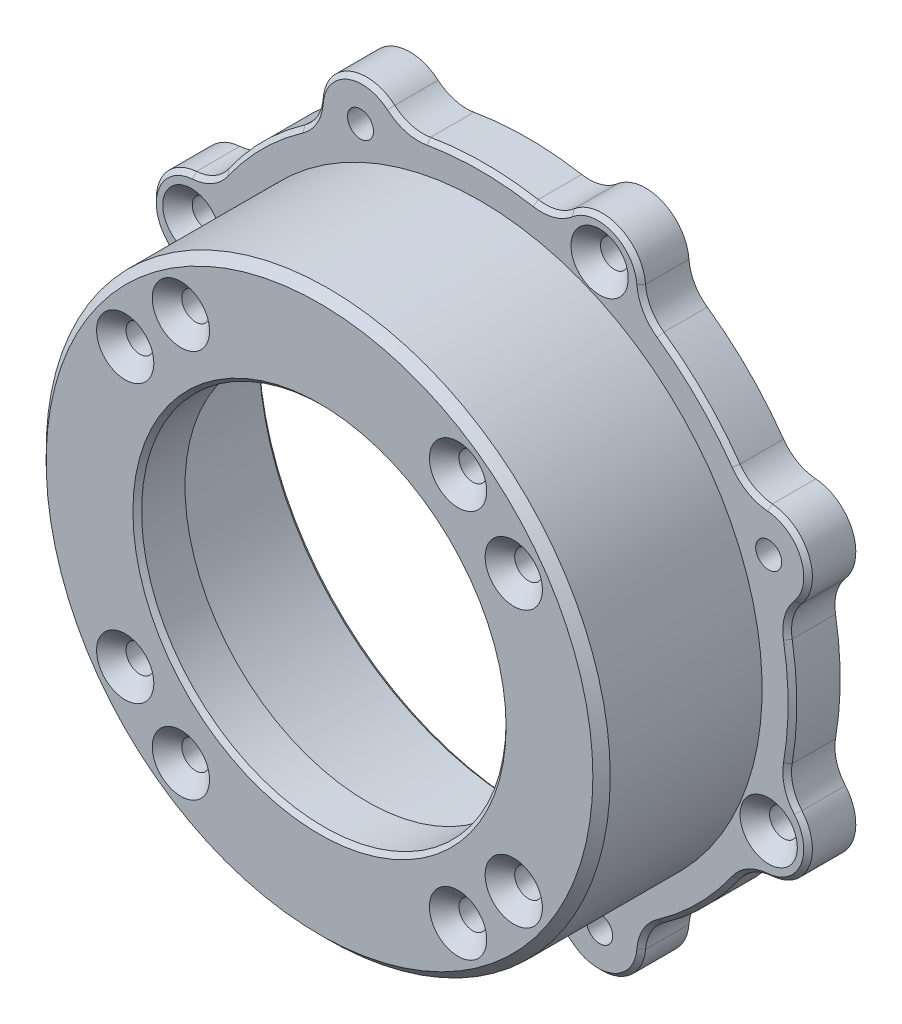
SolidWorks part; units mm, degrees
material "6061 合金"
ref_plane "前视基准面" through (0, 0, 0) normal (0, 0, 1) x (1, 0, 0)
ref_plane "上视基准面" through (0, 0, 0) normal (0, 1, 0) x (1, 0, 0)
ref_plane "右视基准面" through (0, 0, 0) normal (1, 0, 0) x (0, 0, -1)
sketch "草图2" plane through (0, 0, 0) normal (0, 0, 1) x (1, 0, 0)
  circle A0 centre (-15.9693, -22.3882) radius 1.5
  circle A1 centre (-22.3882, -15.9693) radius 1.5
  circle A2 centre (-22.3882, 15.9693) radius 1.5
  circle A3 centre (-15.9693, 22.3882) radius 1.5
  circle A4 centre (15.9693, 22.3882) radius 1.5
  circle A5 centre (22.3882, 15.9693) radius 1.5
  circle A6 centre (22.3882, -15.9693) radius 1.5
  circle A7 centre (15.9693, -22.3882) radius 1.5
  circle A8 centre (-13.7766, -33.2597) radius 3.25 construction
  circle A10 centre (0, 0) radius 21
  circle A11 centre (0, 0) radius 32.5
  dimension "D1" = 3
  dimension "D2" = 6.5
  dimension "D3" = 42
  dimension "D4" = 65
extrude "凸台-拉伸1" add sketch "草图2" along normal blind 5.5
sketch "草图3" plane through (0, 0, 0) normal (0, 0, -1) x (-1, 0, 0)
  circle A0 centre (0, 0) radius 30.5
  circle A1 centre (0, 0) radius 32.5
  circle A2 centre (0, 0) radius 32.5 construction
  dimension "D1" = 61
extrude "凸台-拉伸2" add sketch "草图3" along normal up to surface (18.5 mm away)
sketch "草图4" plane through (0, 0, -18.5) normal (0, 0, -1) x (-1, 0, 0)
  arc A2 (-10.3285, 36.5916) -> (-18.5708, 33.1776) centre (-13.5853, 32.7977) ccw
  arc A46 (-18.5708, 33.1776) -> (-20.6836, 29.465) centre (-23.5564, 33.5574) cw
  arc A47 (-20.6836, 29.465) -> (-29.465, 20.6836) centre (0, 0) ccw
  arc A48 (-33.1776, 18.5708) -> (-29.465, 20.6836) centre (-33.5574, 23.5564) ccw
  circle A49 centre (-13.7766, 33.2597) radius 1.5
  arc A50 (-10.3285, 36.5916) -> (-18.5708, 33.1776) centre (-13.5853, 32.7977) ccw construction
  circle A51 centre (-13.7766, 33.2597) radius 1.5 construction
  arc A52 (18.5708, 33.1776) -> (10.3285, 36.5916) centre (13.5853, 32.7977) ccw
  circle A53 centre (13.7766, 33.2597) radius 1.5
  arc A54 (10.3285, 36.5916) -> (6.2094, 35.4605) centre (7.0718, 40.3855) cw
  arc A55 (6.2094, 35.4605) -> (-6.2094, 35.4605) centre (0, 0) ccw
  arc A56 (-10.3285, 36.5916) -> (-6.2094, 35.4605) centre (-7.0718, 40.3855) ccw
  arc A57 (36.5916, 10.3285) -> (33.1776, 18.5708) centre (32.7977, 13.5853) ccw
  circle A58 centre (33.2597, 13.7766) radius 1.5
  arc A59 (33.1776, 18.5708) -> (29.465, 20.6836) centre (33.5574, 23.5564) cw
  arc A60 (29.465, 20.6836) -> (20.6836, 29.465) centre (0, 0) ccw
  arc A61 (18.5708, 33.1776) -> (20.6836, 29.465) centre (23.5564, 33.5574) ccw
  arc A62 (33.1776, -18.5708) -> (36.5916, -10.3285) centre (32.7977, -13.5853) ccw
  circle A63 centre (33.2597, -13.7766) radius 1.5
  arc A64 (36.5916, -10.3285) -> (35.4605, -6.2094) centre (40.3855, -7.0718) cw
  arc A65 (35.4605, -6.2094) -> (35.4605, 6.2094) centre (0, 0) ccw
  arc A66 (36.5916, 10.3285) -> (35.4605, 6.2094) centre (40.3855, 7.0718) ccw
  arc A67 (10.3285, -36.5916) -> (18.5708, -33.1776) centre (13.5853, -32.7977) ccw
  circle A68 centre (13.7766, -33.2597) radius 1.5
  arc A69 (18.5708, -33.1776) -> (20.6836, -29.465) centre (23.5564, -33.5574) cw
  arc A70 (20.6836, -29.465) -> (29.465, -20.6836) centre (0, 0) ccw
  arc A71 (33.1776, -18.5708) -> (29.465, -20.6836) centre (33.5574, -23.5564) ccw
  arc A72 (-18.5708, -33.1776) -> (-10.3285, -36.5916) centre (-13.5853, -32.7977) ccw
  circle A73 centre (-13.7766, -33.2597) radius 1.5
  arc A74 (-10.3285, -36.5916) -> (-6.2094, -35.4605) centre (-7.0718, -40.3855) cw
  arc A75 (-6.2094, -35.4605) -> (6.2094, -35.4605) centre (0, 0) ccw
  arc A76 (10.3285, -36.5916) -> (6.2094, -35.4605) centre (7.0718, -40.3855) ccw
  arc A77 (-36.5916, -10.3285) -> (-33.1776, -18.5708) centre (-32.7977, -13.5853) ccw
  circle A78 centre (-33.2597, -13.7766) radius 1.5
  arc A79 (-33.1776, -18.5708) -> (-29.465, -20.6836) centre (-33.5574, -23.5564) cw
  arc A80 (-29.465, -20.6836) -> (-20.6836, -29.465) centre (0, 0) ccw
  arc A81 (-18.5708, -33.1776) -> (-20.6836, -29.465) centre (-23.5564, -33.5574) ccw
  arc A82 (-33.1776, 18.5708) -> (-36.5916, 10.3285) centre (-32.7977, 13.5853) ccw
  circle A83 centre (-33.2597, 13.7766) radius 1.5
  arc A84 (-36.5916, 10.3285) -> (-35.4605, 6.2094) centre (-40.3855, 7.0718) cw
  arc A85 (-35.4605, 6.2094) -> (-35.4605, -6.2094) centre (0, 0) ccw
  arc A86 (-36.5916, -10.3285) -> (-35.4605, -6.2094) centre (-40.3855, -7.0718) ccw
  circle A87 centre (0, 0) radius 30.5
  circle A88 centre (0, 0) radius 30.5 construction
  point P94 (0, 0)
extrude "凸台-拉伸3" add sketch "草图4" against normal blind 5.5
chamfer "倒角1" distance 1 angle 45 1 edges at (32.5, 0, 5.5)
chamfer "倒角3" distance 0.5 angle 45 34 edges at (19.2108, 31.0843, -13) (0, 30.5, -18.5) (-37.4171, 15.4987, -13) (-31.0843, 19.2108, -13) (-35.564, 8.3958, -13) (-25.4558, 25.4558, -13) (-36, 0, -13) (-19.2108, 31.0843, -13) (-35.564, -8.3958, -13) (-15.4987, 37.4171, -13) (-37.4171, -15.4987, -13) (-8.3958, 35.564, -13) (-31.0843, -19.2108, -13) (0, 36, -13) (-25.4558, -25.4558, -13) (8.3958, 35.564, -13) (-19.2108, -31.0843, -13) (15.4987, 37.4171, -13) (-15.4987, -37.4171, -13) (-8.3958, -35.564, -13) (25.4558, 25.4558, -13) (0, -36, -13) (31.0843, 19.2108, -13) (8.3958, -35.564, -13) (37.4171, 15.4987, -13) (15.4987, -37.4171, -13) (35.564, 8.3958, -13) (19.2108, -31.0843, -13) (36, 0, -13) (25.4558, -25.4558, -13) (35.564, -8.3958, -13) (31.0843, -19.2108, -13) (37.4171, -15.4987, -13) (21, 0, 5.5)
hole_wizard "打孔尺寸(%根据十字)槽沉头木螺钉的类型0" positions "草图5" profile "草图6" countersink size "M3" standard "GB"
sketch "草图5" plane through (0, 0, -13) normal (0, 0, 1) x (1, 0, 0)
  point P0 (13.7766, 33.2597)
  point P6 (33.2597, -13.7766)
  point P12 (-13.7766, -33.2597)
  point P18 (-33.2597, 13.7766)
sketch "草图6" plane through (13.7766, 33.2597, -13) normal (1, 0, 0) x (0, -1, 0)
  line L0 (0, 0) -> (0, 9.0614)
  line L1 (0, 9.0614) -> (1.6, 8.1)
  line L2 (1.6, 8.1) -> (1.6, 1.7)
  line L3 (1.6, 1.7) -> (3.3, 0)
  line L5 (3.3, 0) -> (0, 0)
  line L6 (-1.6, 1.7) -> (-3.3, 0) construction
  line L10 (0, 9.0614) -> (-1.6, 8.1) construction
  line L11 (0, -6.35) -> (0, 107.95) construction
  dimension "孔直径" = 3.2
  dimension "孔深度" = 8.1
  dimension "近端锥形沉头孔直径" = 6.6
  dimension "近端锥形沉头孔角度" = 90
  dimension "导头角度" = 118
hole_wizard "打孔尺寸(%根据十字)槽沉头木螺钉的类型1" positions "草图7" profile "草图8" countersink size "M3" standard "GB"
sketch "草图7" plane through (0, 0, 5.5) normal (0, 0, 1) x (1, 0, 0)
  point P0 (-15.9693, 22.3882)
  point P3 (-22.3882, 15.9693)
  point P6 (-22.3882, -15.9693)
  point P9 (-15.9693, -22.3882)
  point P12 (15.9693, -22.3882)
  point P15 (22.3882, -15.9693)
  point P18 (22.3882, 15.7463)
  point P20 (15.9693, 22.3882)
sketch "草图8" plane through (-15.9693, 22.3882, 5.5) normal (1, 0, 0) x (0, -1, 0)
  line L0 (0, 0) -> (0, 9.0614)
  line L1 (0, 9.0614) -> (1.6, 8.1)
  line L2 (1.6, 8.1) -> (1.6, 1.7)
  line L3 (1.6, 1.7) -> (3.3, 0)
  line L5 (3.3, 0) -> (0, 0)
  line L6 (-1.6, 1.7) -> (-3.3, 0) construction
  line L10 (0, 9.0614) -> (-1.6, 8.1) construction
  line L11 (0, -6.35) -> (0, 107.95) construction
  dimension "孔直径" = 3.2
  dimension "孔深度" = 8.1
  dimension "近端锥形沉头孔直径" = 6.6
  dimension "近端锥形沉头孔角度" = 90
  dimension "导头角度" = 118
